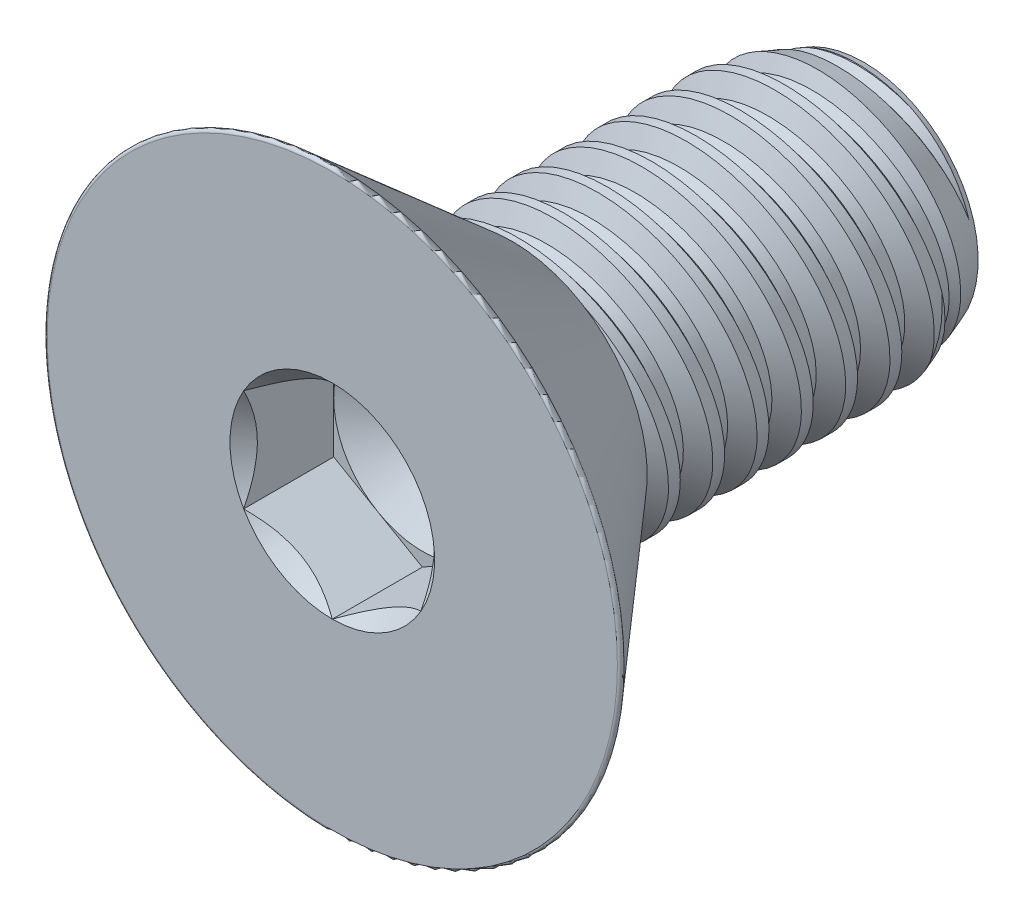
SolidWorks part; units mm, degrees
material "AISI 4340 Steel, normalized"
ref_plane "Front" through (0, 0, 0) normal (0, 0, 1) x (1, 0, 0)
ref_plane "Top" through (0, 0, 0) normal (0, 1, 0) x (1, 0, 0)
ref_plane "Right" through (0, 0, 0) normal (1, 0, 0) x (0, 0, -1)
sketch "Sketch1" plane through (0, 0, 0) normal (1, 0, 0) x (0, 0, -1)
  line L0 (0, 0) -> (-3.2258, 0) construction
  line L1 (0, 0) -> (6.2992, 0)
  line L2 (0, 0) -> (0, 2.413)
  line L3 (0, 2.413) -> (6.2992, 2.413)
  line L4 (6.2992, 0) -> (6.2992, 2.413)
  line L5 (0, -2.413) -> (6.2992, -2.413) construction
  dimension "D1" = 6.2992
  dimension "Thread Dia" = 4.826
  dimension "Length" = 9.525
  dimension "Head Height" = 3.2258
revolve "Revolve1" add sketch "Sketch1" angle 360 about L0
ref_plane "Plane1" through (0, 0, 3.2258) normal (0, 0, 1) x (1, 0, 0)
sketch "Sketch2" plane through (0, 0, 0) normal (1, 0, 0) x (0, 0, -1)
  line L0 (0, 2.413) -> (0, -2.413) construction
  line L1 (0, -2.413) -> (0.7938, -2.413) construction
  line L2 (0.7938, -2.413) -> (0, 2.413) construction
  line L3 (0, 2.413) -> (0.0979, 2.4291) construction
  line L4 (0.0979, 2.4291) -> (0.7832, 2.5418)
  line L5 (0.7832, 2.5418) -> (0.6082, 2.0776)
  line L6 (0.6082, 2.0776) -> (0.4124, 2.0454)
  line L7 (0.4124, 2.0454) -> (0.0979, 2.4291)
  line L8 (0.5103, 2.0615) -> (0.4406, 2.4855) construction
  line L9 (0, -2.413) -> (6.2992, -2.413) construction
  line L10 (0, 2.413) -> (6.2992, 2.413) construction
  line L12 (0.4525, 2.413) -> (1.2462, -2.413) construction
  line L13 (0, -0.1397) -> (1.6987, 0.1397) construction
  line L15 (0, 0) -> (0, 2.413) construction
  point P19 (0.8494, 0)
  dimension "D1" = 60
  dimension "Thread Pitch" = 0.7937
  dimension "D2" = 0.0992
  dimension "D3" = 0.1984
  dimension "D4" = 0.7937
revolve "Cut-Revolve1" cut sketch "Sketch2" angle 360 about L13
sketch "Sketch3" plane through (0, 0, 0) normal (1, 0, 0) x (0, 0, -1)
  line L0 (6.2992, 2.0454) -> (5.2893, 2.413)
  line L1 (5.2893, 2.413) -> (6.2992, 2.413)
  line L2 (6.2992, 2.413) -> (6.2992, 2.0454)
  line L3 (0, 2.413) -> (6.2992, 2.413) construction
  line L4 (6.2992, 0) -> (6.2992, 2.413) construction
  line L5 (5.2893, 0) -> (0, 0) construction
  line L6 (5.2893, 2.413) -> (5.2893, -2.413) construction
  line L7 (0, -2.413) -> (6.2992, -2.413) construction
  dimension "D1" = 20
  dimension "D2" = 4.826
revolve "Cut-Revolve2" cut sketch "Sketch3" angle 360 about L5
pattern_linear "LPattern1" count 8 spacing 0.7937 along (0, 0, 1)
pattern_linear "LPattern2" count 2 spacing 0.7937 along (0, 0, 1)
sketch "Sketch4" plane through (0, 0, 0) normal (0, 0, 1) x (1, 0, 0)
  circle A0 centre (0, 0) radius 5.2197
  dimension "Head Dia" = 10.4394
extrude "Extrude1" add sketch "Sketch4" along normal up to surface (3.2258 mm away)
sketch "Sketch9" plane through (0, 0, 0) normal (1, 0, 0) x (0, 0, -1)
  line L0 (-3.2258, 5.2197) -> (0, 2.4156)
  line L1 (0, 2.4156) -> (0, 5.2197)
  line L2 (0, 5.2197) -> (-3.2258, 5.2197)
  line L3 (0, 0) -> (-3.2258, 0) construction
  line L6 (-3.2258, -5.2197) -> (0, -2.4156) construction
  line L7 (0, -5.2197) -> (0, 5.2197) construction
  line L8 (-3.2258, 5.2197) -> (-3.2258, -5.2197) construction
  line L9 (0, 5.2197) -> (-3.2258, 5.2197) construction
  dimension "D1" = 82
revolve "Cut-Revolve3" cut sketch "Sketch9" angle 360 about L3
fillet "Fillet1" radius 0.0508
sketch "Sketch6" plane through (0, 0, 3.2258) normal (0, 0, 1) x (1, 0, 0)
  line L1 (0, -1.8331) -> (1.5875, -0.9165)
  line L2 (1.5875, -0.9165) -> (1.5875, 0.9165)
  line L3 (1.5875, 0.9165) -> (0, 1.8331)
  line L4 (0, 1.8331) -> (-1.5875, 0.9165)
  line L5 (-1.5875, 0.9165) -> (-1.5875, -0.9165)
  line L6 (-1.5875, -0.9165) -> (0, -1.8331)
  circle A0 centre (0, 0) radius 1.5875 construction
  dimension "Hex" = 3.175
extrude "Cut-Extrude1" cut sketch "Sketch6" against normal blind 1.6129
sketch "Sketch7" plane through (0, 0, 3.2258) normal (0, 0, 1) x (1, 0, 0)
  circle A0 centre (0, 0) radius 1.8331
extrude "Cut-Extrude4" cut sketch "Sketch7" against normal blind 1.6129 draft 45
sketch "Sketch8" plane through (0, 0, 1.6129) normal (0, 0, 1) x (1, 0, 0)
  circle A0 centre (0, 0) radius 1.5875 construction
  circle A1 centre (0, 0) radius 1.5875
extrude "Cut-Extrude5" cut sketch "Sketch8" against normal blind 0.5376 draft 60
equation "\"D2@Sketch2\"=\"Thread Pitch@Sketch2\"/8"
equation "\"D3@Sketch2\"=\"Thread Pitch@Sketch2\"/4"
equation "\"D4@Sketch2\"=\"Thread Pitch@Sketch2\""
equation "\"D3@LPattern1\"=\"Thread Pitch@Sketch2\""
equation "\"D1@Cut-Extrude1\"=\"Head Height@Sketch1\"/2"
equation "\"D1@Cut-Extrude4\"=\"D1@Cut-Extrude1\""
equation "\"D1@Cut-Extrude5\"=\"D1@Cut-Extrude1\"/3"
equation "\"D1@LPattern1\"=\"D1@Sketch1\"/\"Thread Pitch@Sketch2\""
equation "\"D3@LPattern2\"=\"Thread Pitch@Sketch2\""
